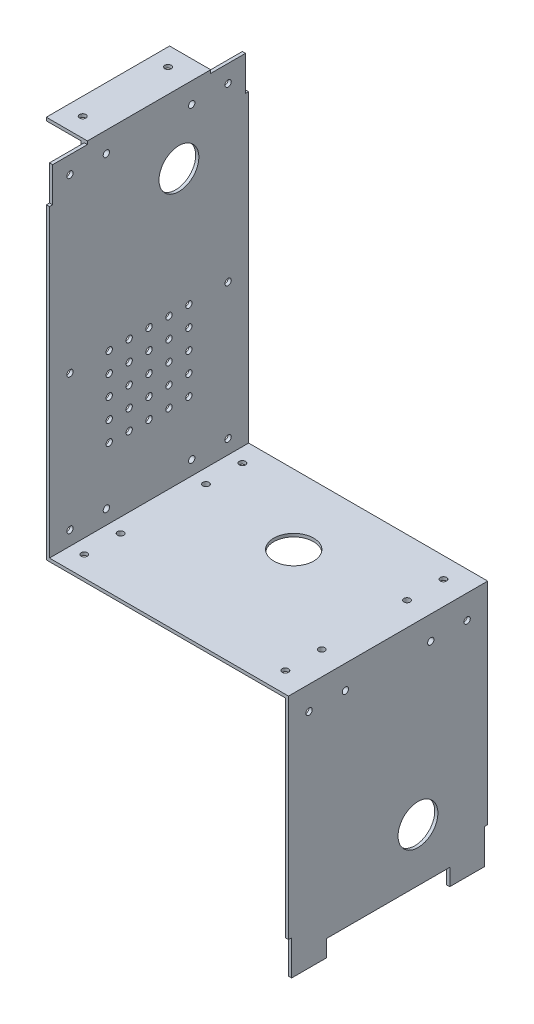
SolidWorks part; units mm, degrees
ref_plane "Plan de face" through (0, 0, 0) normal (0, 0, 1) x (1, 0, 0)
ref_plane "Plan de dessus" through (0, 0, 0) normal (0, 1, 0) x (1, 0, 0)
ref_plane "Plan de droite" through (0, 0, 0) normal (1, 0, 0) x (0, 0, -1)
sketch "Esquisse1" plane through (0, 0, 0) normal (0, 0, 1) x (1, 0, 0)
  line L0 (-113.8505, 166.8349) -> (-113.8505, -6.5826)
  line L1 (-113.8505, -6.5826) -> (6.1495, -6.5826)
  line L2 (6.1495, -6.5826) -> (6.1495, -129.9413)
  line L3 (6.1495, -129.9413) -> (7.737, -129.9413)
  line L4 (7.737, -129.9413) -> (7.737, -4.9951)
  line L5 (7.737, -4.9951) -> (-112.263, -4.9951)
  line L6 (-112.263, -4.9951) -> (-112.263, 166.8349)
  line L7 (-112.263, 166.8349) -> (-113.8505, 166.8349)
  dimension "D1" = 173.4175
  dimension "D2" = 1.5875
  dimension "D3" = 1.5875
  dimension "D4" = 1.5875
  dimension "D5" = 120
  dimension "D6" = 123.3588
extrude "Boss.-Extru.1" add sketch "Esquisse1" along normal blind 100
sketch "Esquisse2" plane through (0, -6.5826, 0) normal (0, -1, 0) x (1, 0, 0)
  line L0 (-113.8505, 100) -> (6.1495, 100) construction
  line L1 (-96.388, 80.95) -> (-115.438, 80.95)
  line L2 (-96.388, 80.95) -> (-96.388, 19.05)
  line L3 (-96.388, 19.05) -> (-115.438, 19.05)
  line L4 (-115.438, 80.95) -> (-115.438, 19.05)
  line L5 (-113.8505, 0) -> (6.1495, 0) construction
  line L6 (-113.8505, 100) -> (-113.8505, 0) construction
  dimension "D1" = 19.05
  dimension "D2" = 19.05
  dimension "D3" = 1.5875
  dimension "D4" = 19.05
extrude "Boss.-Extru.2" add sketch "Esquisse2" along normal blind 1.5875
sketch "Esquisse3" plane through (0, -6.5826, 0) normal (0, 1, 0) x (1, 0, 0)
  line L4 (-113.8505, -80.95) -> (-113.8505, -19.05)
  line L5 (-113.8505, -19.05) -> (-115.438, -19.05)
  line L6 (-115.438, -19.05) -> (-115.438, -80.95)
  line L7 (-115.438, -80.95) -> (-113.8505, -80.95)
  line L8 (-113.8505, -80.95) -> (-113.8505, -19.05)
  line L9 (-113.8505, -19.05) -> (-115.438, -19.05)
  line L10 (-115.438, -19.05) -> (-115.438, -80.95)
  line L11 (-115.438, -80.95) -> (-113.8505, -80.95)
  dimension "D1" = 0
extrude "Boss.-Extru.3" add sketch "Esquisse3" along normal blind 17.4625
sketch "Esquisse4" plane through (6.1495, 0, 0) normal (-1, 0, 0) x (0, 0, 1)
  line L1 (80.95, -6.5826) -> (19.05, -6.5826)
  line L2 (80.95, -6.5826) -> (80.95, -25.6326)
  line L3 (80.95, -25.6326) -> (19.05, -25.6326)
  line L4 (19.05, -6.5826) -> (19.05, -25.6326)
  line L5 (100, -6.5826) -> (100, -129.9413) construction
  line L6 (0, -6.5826) -> (0, -129.9413) construction
  line L7 (100, -6.5826) -> (0, -6.5826) construction
  dimension "D1" = 19.05
  dimension "D2" = 19.05
  dimension "D3" = 19.05
extrude "Boss.-Extru.4" add sketch "Esquisse4" along normal blind 1.5875
sketch "Esquisse5" plane through (4.562, 0, 0) normal (-1, 0, 0) x (0, 0, 1)
  line L0 (80.95, -25.6326) -> (80.95, -6.5826) construction
  line L1 (19.05, -6.5826) -> (80.95, -6.5826)
  line L2 (19.05, -6.5826) -> (19.05, -8.1701)
  line L3 (19.05, -8.1701) -> (80.95, -8.1701)
  line L4 (80.95, -6.5826) -> (80.95, -8.1701)
  dimension "D1" = 1.5875
extrude "Boss.-Extru.5" add sketch "Esquisse5" along normal blind 17.4625
sketch "Esquisse7" plane through (-113.8505, 0, 0) normal (-1, 0, 0) x (0, 0, 1)
  line L0 (80.95, 10.8799) -> (80.95, -6.5826) construction
  line L1 (80.95, 166.8349) -> (19.05, 166.8349)
  line L2 (80.95, 166.8349) -> (80.95, 147.7849)
  line L3 (80.95, 147.7849) -> (19.05, 147.7849)
  line L4 (19.05, 166.8349) -> (19.05, 147.7849)
  line L5 (19.05, 10.8799) -> (19.05, -6.5826) construction
  line L6 (100, 166.8349) -> (0, 166.8349) construction
  line L7 (80.95, -8.1701) -> (80.95, 10.8799) construction
extrude "Boss.-Extru.6" add sketch "Esquisse7" along normal blind 1.5875
sketch "Esquisse8" plane through (-115.438, 0, 0) normal (-1, 0, 0) x (0, 0, 1)
  line L0 (19.05, 166.8349) -> (19.05, 147.7849) construction
  line L1 (80.95, 166.8349) -> (19.05, 166.8349)
  line L2 (80.95, 166.8349) -> (80.95, 165.2474)
  line L3 (80.95, 165.2474) -> (19.05, 165.2474)
  line L4 (19.05, 166.8349) -> (19.05, 165.2474)
  dimension "D1" = 1.5875
extrude "Boss.-Extru.7" add sketch "Esquisse8" along normal blind 17.4625
sketch "Esquisse11" plane through (-115.438, 0, 0) normal (-1, 0, 0) x (0, 0, 1)
  line L0 (80.95, 147.7849) -> (80.95, 165.2474) construction
  line L1 (50, 165.2474) -> (50, 147.7849) construction
  line L2 (19.05, 165.2474) -> (80.95, 165.2474) construction
  line L3 (19.05, 147.7849) -> (80.95, 147.7849) construction
  line L4 (50, 10.8799) -> (50, -6.5826) construction
  line L5 (19.05, 10.8799) -> (80.95, 10.8799) construction
  line L6 (80.95, -6.5826) -> (19.05, -6.5826) construction
  line L7 (71.425, 156.5162) -> (28.575, 156.5162) construction
  circle A0 centre (71.425, 156.5162) radius 1.5875
  circle A1 centre (28.575, 156.5162) radius 1.5875
  circle A2 centre (71.425, 2.1487) radius 1.5875
  circle A3 centre (28.575, 2.1487) radius 1.5875
  point P10 (50, 156.5162)
  point P21 (50, 156.5162)
  point P24 (50, 2.1487)
  dimension "D2" = 3.175
  dimension "D1" = 9.525
extrude "Enlèv. mat.-Extru.1" cut sketch "Esquisse11" against normal up to next
sketch "Esquisse12" plane through (0, -8.1701, 0) normal (0, -1, 0) x (1, 0, 0)
  line L0 (-105.1193, 71.425) -> (-105.1193, 28.575) construction
  line L1 (-96.388, 80.95) -> (-115.438, 80.95) construction
  line L2 (-115.438, 80.95) -> (-115.438, 19.05) construction
  line L3 (-96.388, 22.3315) -> (-113.8505, 22.3315) construction
  line L5 (-12.9005, 52.2011) -> (4.562, 52.2011) construction
  line L6 (-12.9005, 19.05) -> (-12.9005, 80.95) construction
  line L7 (4.562, 19.05) -> (4.562, 80.95) construction
  line L8 (-96.388, 19.05) -> (-96.388, 80.95) construction
  line L9 (-113.8505, 19.05) -> (-113.8505, 80.95) construction
  circle A0 centre (-105.1193, 71.425) radius 1.5875
  circle A1 centre (-105.1193, 28.575) radius 1.5875
  circle A2 centre (-4.1693, 71.425) radius 1.5875
  circle A3 centre (-4.1693, 28.575) radius 1.5875
  point P8 (-105.1193, 50)
  point P13 (-115.438, 50)
  point P26 (-4.1693, 52.2011)
  point P28 (-105.1193, 22.3315)
  dimension "D2" = 3.175
  dimension "D1" = 9.525
extrude "Enlèv. mat.-Extru.2" cut sketch "Esquisse12" against normal up to next
sketch "Esquisse13" plane through (4.562, 0, 0) normal (-1, 0, 0) x (0, 0, 1)
  line L0 (80.95, -25.6326) -> (80.95, -8.1701) construction
  line L1 (50, -8.1701) -> (50, -25.6326) construction
  line L2 (19.05, -8.1701) -> (80.95, -8.1701) construction
  line L3 (19.05, -25.6326) -> (80.95, -25.6326) construction
  line L4 (71.425, -16.9013) -> (28.575, -16.9013) construction
  circle A0 centre (71.425, -16.9013) radius 1.5875
  circle A1 centre (28.575, -16.9013) radius 1.5875
  point P8 (50, -16.9013)
  dimension "D2" = 3.175
  dimension "D1" = 9.525
extrude "Enlèv. mat.-Extru.3" cut sketch "Esquisse13" against normal up to next
sketch "Esquisse14" plane through (0, 165.2474, 0) normal (0, -1, 0) x (1, 0, 0)
  line L0 (-115.438, 50) -> (-132.9005, 50) construction
  line L1 (-115.438, 19.05) -> (-115.438, 80.95) construction
  line L2 (-132.9005, 19.05) -> (-132.9005, 80.95) construction
  line L3 (-132.9005, 80.95) -> (-115.438, 80.95) construction
  line L4 (-124.1693, 71.425) -> (-124.1693, 28.575) construction
  circle A0 centre (-124.1693, 71.425) radius 1.5875
  circle A1 centre (-124.1693, 28.575) radius 1.5875
  point P10 (-124.1693, 50)
  point P13 (-124.1693, 50)
  dimension "D2" = 3.175
  dimension "D1" = 9.525
extrude "Enlèv. mat.-Extru.4" cut sketch "Esquisse14" against normal up to next contours A0 | A1
sketch "Esquisse16" plane through (-113.8505, 0, 0) normal (-1, 0, 0) x (0, 0, 1)
  line L0 (0, 166.8349) -> (0, -6.5826) construction
  line L1 (19.05, 166.8349) -> (0, 166.8349) construction
  circle A0 centre (35, 131.8349) radius 10
  dimension "D1" = 20
  dimension "D2" = 35
  dimension "D3" = 35
extrude "Enlèv. mat.-Extru.6" cut sketch "Esquisse16" against normal up to next
sketch "Esquisse17" plane through (0, -6.5826, 0) normal (0, -1, 0) x (1, 0, 0)
  line L0 (-113.8505, 0) -> (6.1495, 0) construction
  line L1 (-96.388, 26.6356) -> (-12.9005, 26.6356) construction
  line L2 (-96.388, 19.05) -> (-96.388, 80.95) construction
  line L3 (-12.9005, 80.95) -> (-12.9005, 19.05) construction
  circle A0 centre (-54.6443, 35) radius 10
  point P12 (-54.6443, 26.6356)
  dimension "D1" = 20
  dimension "D2" = 35
extrude "Enlèv. mat.-Extru.7" cut sketch "Esquisse17" against normal up to next
sketch "Esquisse18" plane through (-113.8505, 0, 0) normal (-1, 0, 0) x (0, 0, 1)
  line L0 (50, -6.5826) -> (50, 30.6546) construction
  line L1 (19.05, 147.7849) -> (80.95, 147.7849) construction
  line L2 (0, 166.8349) -> (1.5875, 166.8349)
  line L3 (0, 166.8349) -> (0, 147.7849)
  line L4 (0, 147.7849) -> (1.5875, 147.7849)
  line L6 (0, 166.8349) -> (0, -6.5826) construction
  line L7 (1.5875, 165.2474) -> (1.5875, 147.7849)
  line L8 (1.5875, 165.2474) -> (19.05, 165.2474)
  line L10 (1.5875, 166.8349) -> (19.05, 166.8349)
  line L11 (19.05, 165.2474) -> (19.05, 166.8349)
  line L12 (0, -6.5826) -> (100, -6.5826) construction
  line L13 (98.4125, 165.2474) -> (98.4125, 147.7849)
  line L14 (100, 147.7849) -> (98.4125, 147.7849)
  line L15 (100, 166.8349) -> (100, 147.7849)
  line L16 (100, 166.8349) -> (98.4125, 166.8349)
  line L17 (98.4125, 166.8349) -> (80.95, 166.8349)
  line L18 (98.4125, 165.2474) -> (80.95, 165.2474)
  line L19 (80.95, 165.2474) -> (80.95, 166.8349)
  circle A0 centre (10.3187, 156.5162) radius 1.5875
  circle A1 centre (10.3187, 2.1487) radius 1.5875
  circle A2 centre (10.3187, 70.1987) radius 1.5875
  circle A3 centre (28.575, 156.5162) radius 1.5875 construction
  circle A4 centre (28.575, 156.5162) radius 1.5875 construction
  circle A6 centre (28.575, 2.1487) radius 1.5875 construction
  circle A7 centre (28.575, 2.1487) radius 1.5875 construction
  circle A8 centre (89.6813, 2.1487) radius 1.5875
  circle A9 centre (89.6813, 70.1987) radius 1.5875
  circle A10 centre (89.6813, 156.5162) radius 1.5875
  point P12 (0.7938, 147.7849)
  dimension "D1" = 3.175
  dimension "D2" = 68.05
  dimension "D4" = 10.3187
extrude "Enlèv. mat.-Extru.8" cut sketch "Esquisse18" against normal up to next
sketch "Esquisse19" plane through (6.1495, 0, 0) normal (-1, 0, 0) x (0, 0, 1)
  line L5 (0, -6.5826) -> (0, -129.9413) construction
  line L12 (50, -37.9947) -> (50, -82.6351) construction
  line L13 (100, -129.9413) -> (0, -129.9413) construction
  circle A0 centre (10.3188, -16.9013) radius 1.5875
  circle A2 centre (28.575, -16.9013) radius 1.5875 construction
  circle A4 centre (28.575, -16.9013) radius 1.5875 construction
  circle A6 centre (89.6812, -16.9013) radius 1.5875
  point P28 (50, -129.9413)
  dimension "D3" = 3.175
  dimension "D2" = 10.3187
extrude "Enlèv. mat.-Extru.9" cut sketch "Esquisse19" against normal up to next
sketch "Esquisse20" plane through (0, -6.5826, 0) normal (0, -1, 0) x (1, 0, 0)
  line L0 (-113.8505, 0) -> (6.1495, 0) construction
  line L1 (-77.1148, 50) -> (-32.048, 50) construction
  line L2 (-115.438, 80.95) -> (-115.438, 19.05) construction
  circle A0 centre (-105.1193, 10.3187) radius 1.5875
  circle A1 centre (-4.1693, 10.3187) radius 1.5875
  circle A2 centre (-4.1693, 28.575) radius 1.5875 construction
  circle A3 centre (-105.1193, 28.575) radius 1.5875 construction
  circle A4 centre (-4.1693, 28.575) radius 1.5875 construction
  circle A5 centre (-105.1193, 28.575) radius 1.5875 construction
  circle A6 centre (-4.1693, 89.6813) radius 1.5875
  circle A7 centre (-105.1193, 89.6813) radius 1.5875
  point P14 (-115.438, 50)
  point P21 (0, 0)
  dimension "D2" = 3.175
  dimension "D1" = 10.3187
extrude "Enlèv. mat.-Extru.10" cut sketch "Esquisse20" against normal up to next
sketch "Esquisse21" plane through (-113.8505, 0, 0) normal (-1, 0, 0) x (0, 0, 1)
  line L0 (19.05, 147.7849) -> (80.95, 147.7849) construction
  circle A0 centre (30, 70.1987) radius 1.5875
  circle A1 centre (40, 70.1987) radius 1.5875
  circle A2 centre (50, 70.1987) radius 1.5875
  circle A3 centre (60, 70.1987) radius 1.5875
  circle A4 centre (70, 70.1987) radius 1.5875
  circle A5 centre (40, 60.1987) radius 1.5875
  circle A6 centre (50, 60.1987) radius 1.5875
  circle A7 centre (60, 60.1987) radius 1.5875
  circle A8 centre (70, 60.1987) radius 1.5875
  circle A9 centre (40, 50.1987) radius 1.5875
  circle A10 centre (50, 50.1987) radius 1.5875
  circle A11 centre (60, 50.1987) radius 1.5875
  circle A12 centre (70, 50.1987) radius 1.5875
  circle A13 centre (40, 40.1987) radius 1.5875
  circle A14 centre (50, 40.1987) radius 1.5875
  circle A15 centre (60, 40.1987) radius 1.5875
  circle A16 centre (70, 40.1987) radius 1.5875
  circle A17 centre (40, 30.1987) radius 1.5875
  circle A18 centre (50, 30.1987) radius 1.5875
  circle A19 centre (60, 30.1987) radius 1.5875
  circle A20 centre (70, 30.1987) radius 1.5875
  circle A21 centre (30, 60.1987) radius 1.5875
  circle A22 centre (30, 50.1987) radius 1.5875
  circle A23 centre (30, 40.1987) radius 1.5875
  circle A24 centre (30, 30.1987) radius 1.5875
  circle A25 centre (89.6813, 70.1987) radius 1.5875 construction
  circle A26 centre (89.6813, 70.1987) radius 1.5875 construction
  point P2 (0, 0)
  point P53 (50, 147.7849)
  point P54 (0, 0)
  point P58 (0, 0)
  dimension "D1" = 3.175
  dimension "D2" = 5
extrude "Enlèv. mat.-Extru.11" cut sketch "Esquisse21" against normal up to next (1.5875 mm away)
sketch "Esquisse22" plane through (6.1495, 0, 0) normal (-1, 0, 0) x (0, 0, 1)
  line L0 (0, -6.5826) -> (0, -129.9413) construction
  line L1 (90.8343, -128.3538) -> (90.8343, -129.9413) construction
  line L2 (100, -129.9413) -> (0, -129.9413) construction
  line L3 (0, -129.9413) -> (0, -110.8913)
  line L4 (0, -6.5826) -> (0, -129.9413) construction
  line L5 (0, -110.8913) -> (1.5875, -110.8913)
  line L6 (1.5875, -110.8913) -> (1.5875, -128.3538)
  line L7 (1.5875, -128.3538) -> (19.05, -128.3538)
  line L9 (19.05, -129.9413) -> (0, -129.9413)
  line L10 (100, -129.9413) -> (100, -110.8913)
  line L11 (100, -6.5826) -> (100, -129.9413) construction
  line L12 (100, -110.8913) -> (98.4125, -110.8913)
  line L13 (98.4125, -110.8913) -> (98.4125, -128.3538)
  line L14 (98.4125, -128.3538) -> (80.95, -128.3538)
  line L16 (19.05, -129.9413) -> (100, -129.9413)
  line L17 (19.05, -128.3538) -> (19.05, -119.9413)
  line L18 (19.05, -119.9413) -> (80.95, -119.9413)
  line L19 (80.95, -119.9413) -> (80.95, -128.3538)
  line L20 (11.2531, -128.3538) -> (11.2531, -129.9413) construction
  circle A0 centre (35, -93.3538) radius 10
  dimension "D1" = 20
  dimension "D2" = 35
  dimension "D3" = 36.5875
  dimension "D4" = 1.5875
  dimension "D5" = 19.05
  dimension "D6" = 10
extrude "Enlèv. mat.-Extru.12" cut sketch "Esquisse22" against normal up to next
